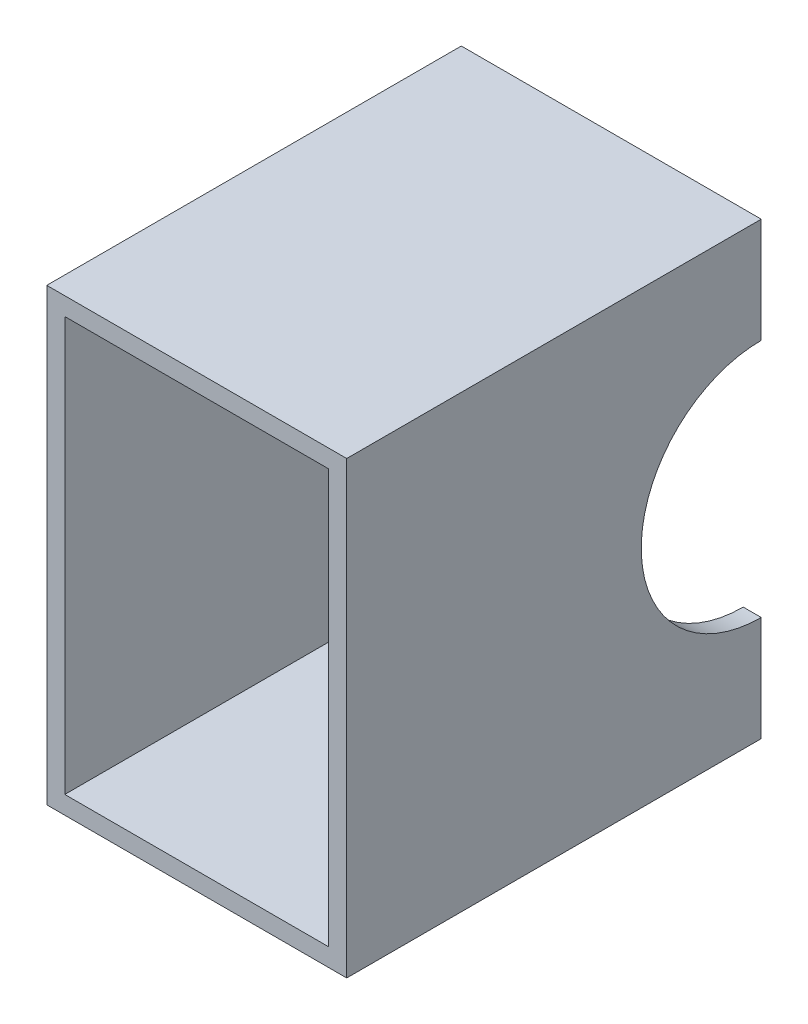
SolidWorks part; units mm, degrees
material "Plain Carbon Steel"
ref_plane "Front Plane" through (0, 0, 0) normal (0, 0, 1) x (1, 0, 0)
ref_plane "Top Plane" through (0, 0, 0) normal (0, 1, 0) x (1, 0, 0)
ref_plane "Right Plane" through (0, 0, 0) normal (1, 0, 0) x (0, 0, -1)
sketch "Sketch1" plane through (0, 0, 0) normal (0, 0, 1) x (1, 0, 0)
  line B0 (-50, -75) -> (50, -75)
  line B1 (-50, -75) -> (-50, 75)
  line B2 (50, -75) -> (50, 75)
  line B3 (-50, 75) -> (50, 75)
  line B4 (-44, -69) -> (44, -69)
  line B5 (-44, -69) -> (-44, 69)
  line B6 (44, -69) -> (44, 69)
  line B7 (-44, 69) -> (44, 69)
sketch_block_instance "15x10x6_profil-1"
sketch_block "15x10x6_profil" parameters "D1"=100, "D2"=150, "D3"=6, "D4"=6
extrude "Boss-Extrude1" add sketch "Sketch1" along normal blind 138.2023
sketch "Sketch2" plane through (0, 0, 0) normal (1, 0, 0) x (0, 0, -1)
  circle A0 centre (0, 0) radius 40
  dimension "D1" = 80
extrude "Cut-Extrude1" cut sketch "Sketch2" against normal through all and the other way through all
